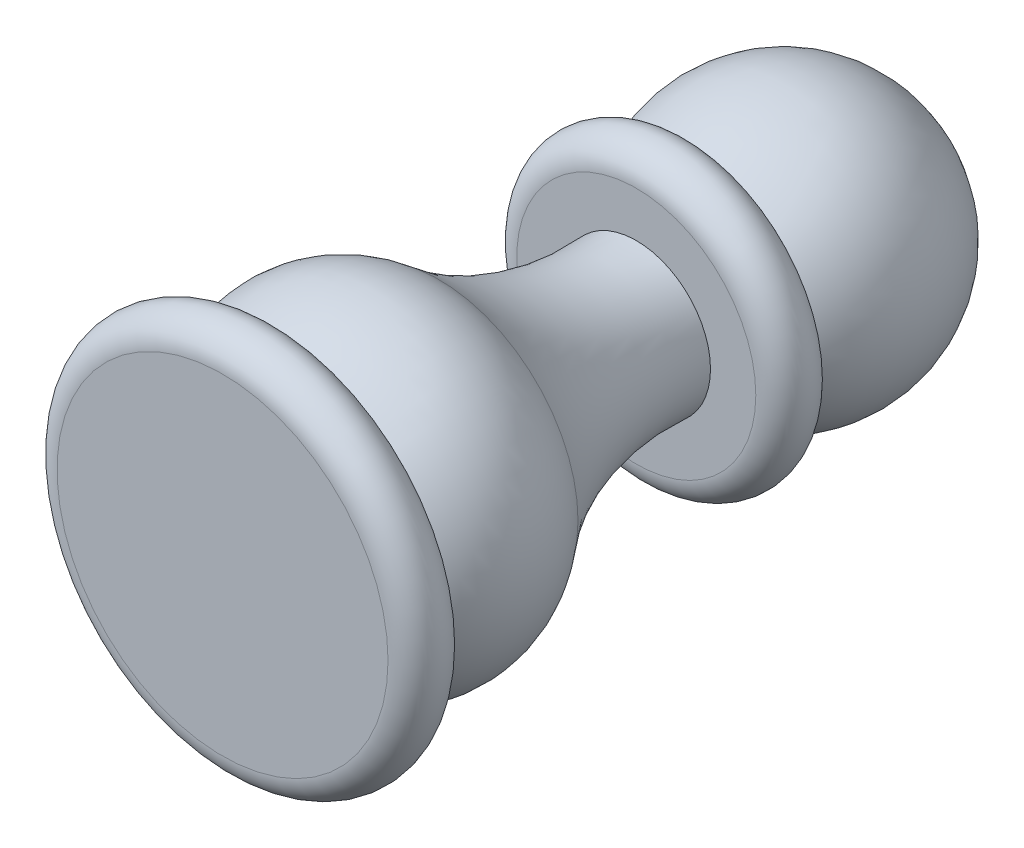
SolidWorks part; units mm, degrees
ref_plane "Front Plane" through (0, 0, 0) normal (0, 0, 1) x (1, 0, 0)
ref_plane "Top Plane" through (0, 0, 0) normal (0, 1, 0) x (1, 0, 0)
ref_plane "Right Plane" through (0, 0, 0) normal (1, 0, 0) x (0, 0, -1)
sketch "Sketch1" plane through (0, 0, 0) normal (1, 0, 0) x (0, 0, -1)
  line L0 (0, 0) -> (27.8888, 0) construction
  line L1 (0, 0) -> (0, -9)
  line L2 (3, -9) -> (3, 0)
  line L3 (6.0987, -9) -> (3, -9) construction
  line L4 (3, 0) -> (3, -6.5)
  line L5 (22.5, -4.0351) -> (22.5, 0)
  line L6 (22.5, 0) -> (22.5, -6.5)
  line L7 (25.5, -6.5) -> (25.5, 0)
  line L8 (21.4749, -4) -> (3, -4) construction
  line L9 (25.5, 0) -> (38, 0) construction
  line L10 (0, 0) -> (38, 0)
  arc A0 (0, -9) -> (3, -9) centre (1.5, -9) ccw
  arc A3 (3, -6.5) -> (11.7595, -7.5714) centre (7.8734, -3) ccw
  arc A4 (11.7595, -7.5714) -> (22.5, -4.0351) centre (21.4749, -19) cw
  arc A5 (22.5, -6.5) -> (25.5, -6.5) centre (24, -6.5) ccw
  arc A6 (25.5, -5.5902) -> (38, 0) centre (30.5, 0) ccw
  dimension "D2" = 1.5
  dimension "D3" = 6.5
  dimension "D5" = 6
  dimension "D6" = 6
  dimension "D7" = 15
  dimension "D8" = 1.5
  dimension "D11" = 15
  dimension "D12" = 5
  dimension "D1" = 9
  dimension "D4" = 9
  dimension "D9" = 6.5
  dimension "D10" = 4
  dimension "D13" = 38
revolve "Revolve1" add sketch "Sketch1" angle 360 about L10
